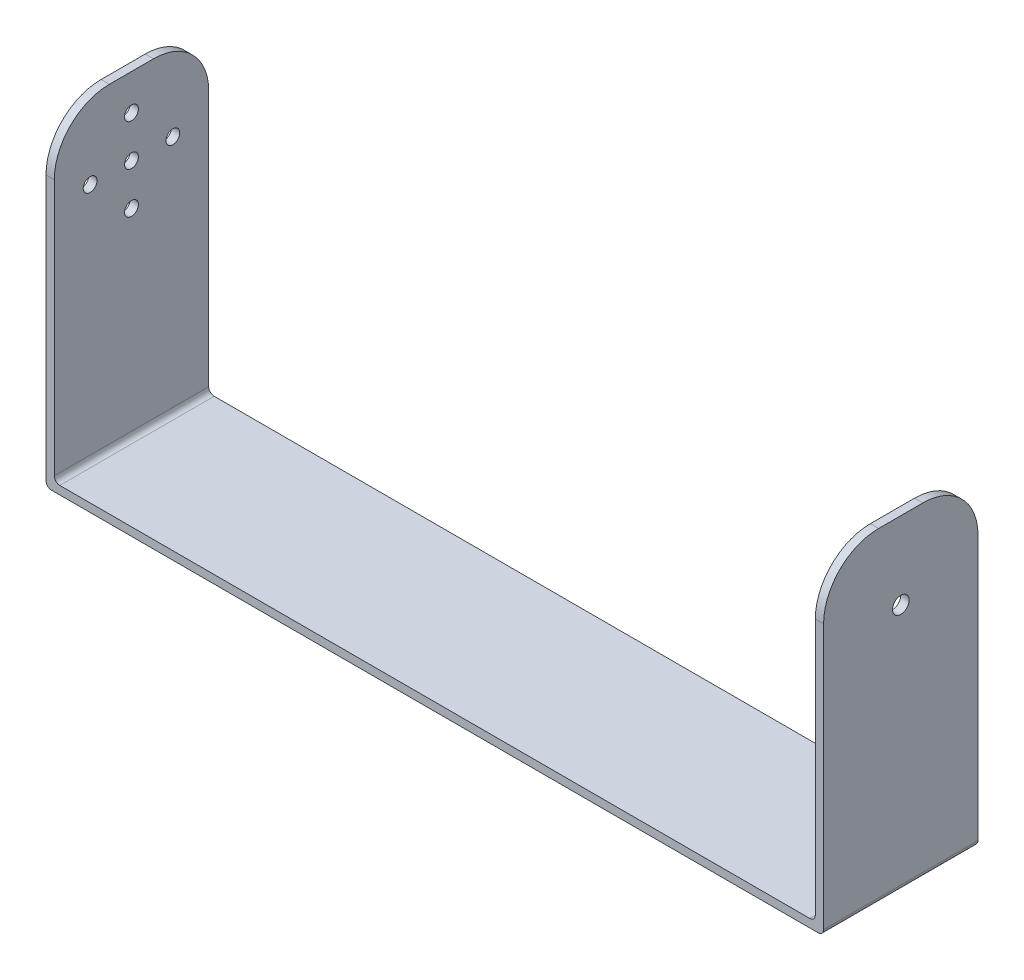
SolidWorks part; units mm, degrees
ref_plane "Front Plane" through (0, 0, 0) normal (0, 0, 1) x (1, 0, 0)
ref_plane "Top Plane" through (0, 0, 0) normal (0, 1, 0) x (1, 0, 0)
ref_plane "Right Plane" through (0, 0, 0) normal (1, 0, 0) x (0, 0, -1)
sketch "Sketch1" plane through (0, 0, 0) normal (0, 1, 0) x (1, 0, 0)
  line L1 (0, 0) -> (138, 0)
  line L2 (0, 0) -> (0, 28)
  line L3 (0, 28) -> (138, 28)
  line L4 (138, 0) -> (138, 28)
  dimension "D1" = 28
  dimension "D2" = 138
extrude "Boss-Extrude1" add sketch "Sketch1" along normal blind 1.5
sketch "Sketch2" plane through (0, 0, 0) normal (1, 0, 0) x (0, 0, -1)
  line L1 (0, 0) -> (28, 0)
  line L2 (0, 0) -> (0, 59)
  line L3 (0, 59) -> (28, 59)
  line L4 (28, 0) -> (28, 59)
  dimension "D1" = 28
  dimension "D2" = 59
extrude "Boss-Extrude2" add sketch "Sketch2" against normal blind 1.5
fillet "Fillet1" radius 1 1 edges
fillet "Fillet2" radius 1 1 edges at (-1.5, 0, -14)
fillet "Fillet5" radius 10 2 edges at (-0.75, 59, 0) (-0.75, 59, -28)
sketch "Sketch3" plane through (0, 0, 0) normal (1, 0, 0) x (0, 0, -1)
  line L0 (18, 59) -> (10, 59) construction
  line L1 (0, 49) -> (0, 2.5) construction
  line L2 (28, 2.5) -> (28, 49) construction
  circle A0 centre (14, 52.5) radius 1.25
  circle A1 centre (6.5, 45) radius 1.25
  circle A2 centre (14, 45) radius 1.25
  circle A3 centre (21.5, 45) radius 1.25
  circle A4 centre (14, 37.5) radius 1.25
  dimension "D1" = 14
  dimension "D2" = 7.5
  dimension "D3" = 7.5
  dimension "D4" = 14
  dimension "D5" = 7.5
  dimension "D6" = 14
  dimension "D8" = 7.5
  dimension "D10" = 14
extrude "Cut-Extrude1" cut sketch "Sketch3" against normal blind 15 and the other way blind 15
sketch "Sketch4" plane through (138, 0, 0) normal (1, 0, 0) x (0, 0, -1)
  line L1 (28, 0) -> (0, 0)
  line L2 (28, 0) -> (28, 59)
  line L3 (28, 59) -> (0, 59)
  line L4 (0, 0) -> (0, 59)
  dimension "D1" = 59
  dimension "D2" = 28
extrude "Boss-Extrude3" add sketch "Sketch4" along normal blind 1.5
fillet "Fillet6" radius 1 1 edges at (139.5, 0, -14)
fillet "Fillet7" radius 1 1 edges
sketch "Sketch5" plane through (139.5, 0, 0) normal (1, 0, 0) x (0, 0, -1)
  line L0 (28, 59) -> (0, 59) construction
  line L1 (0, 59) -> (0, 1) construction
  circle A0 centre (14, 45) radius 1.5
  point P2 (14, 59)
  dimension "D1" = 14
  dimension "D2" = 14
extrude "Cut-Extrude3" cut sketch "Sketch5" against normal blind 31.5 and the other way blind 1.5 contours A0
fillet "Fillet10" radius 10 1 edges at (138.75, 59, -28)
fillet "Fillet11" radius 10 1 edges at (138.75, 59, 0)
